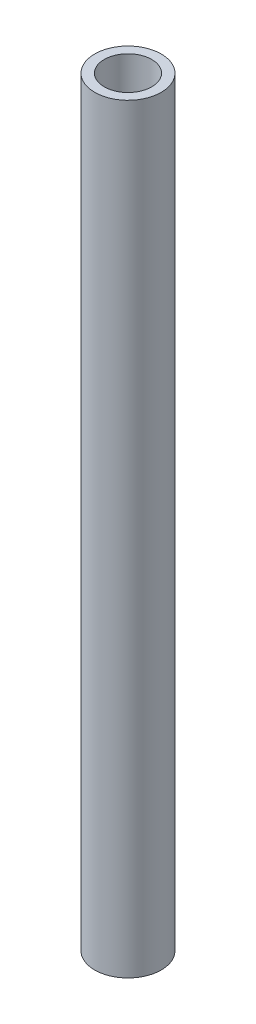
SolidWorks part; units mm, degrees
ref_plane "前视基准面" through (0, 0, 0) normal (0, 0, 1) x (1, 0, 0)
ref_plane "上视基准面" through (0, 0, 0) normal (0, 1, 0) x (1, 0, 0)
ref_plane "右视基准面" through (0, 0, 0) normal (1, 0, 0) x (0, 0, -1)
sketch "草图1" plane through (0, 0, 0) normal (0, 1, 0) x (1, 0, 0)
  circle A0 centre (0, 0) radius 3.5
  circle A1 centre (0, 0) radius 2.5
  dimension "D1" = 7
  dimension "D2" = 5
extrude "凸台-拉伸1" add sketch "草图1" along normal mid plane 80
